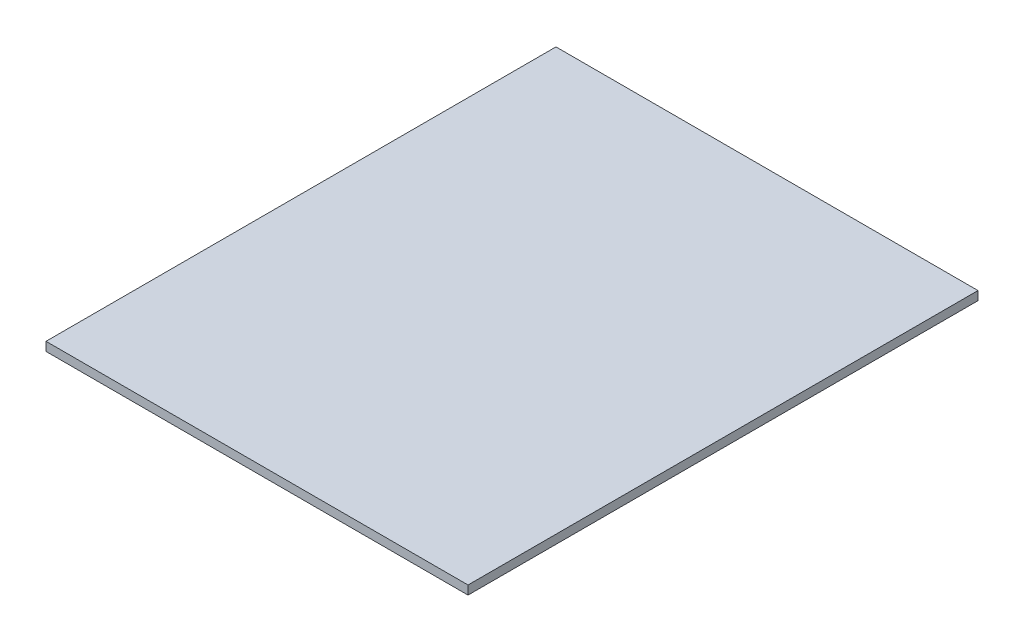
SolidWorks part; units mm, degrees
ref_plane "Front Plane" through (0, 0, 0) normal (0, 0, 1) x (1, 0, 0)
ref_plane "Top Plane" through (0, 0, 0) normal (0, 1, 0) x (1, 0, 0)
ref_plane "Right Plane" through (0, 0, 0) normal (1, 0, 0) x (0, 0, -1)
sketch "Sketch1" plane through (0, 0, 0) normal (0, 1, 0) x (1, 0, 0)
  line L1 (-32.2227, 333.0112) -> (255.7773, 333.0112)
  line L2 (-32.2227, 333.0112) -> (-32.2227, -14.9888)
  line L3 (-32.2227, -14.9888) -> (255.7773, -14.9888)
  line L4 (255.7773, 333.0112) -> (255.7773, -14.9888)
  dimension "D1" = 348
  dimension "D2" = 288
extrude "Boss-Extrude1" add sketch "Sketch1" along normal blind 6
